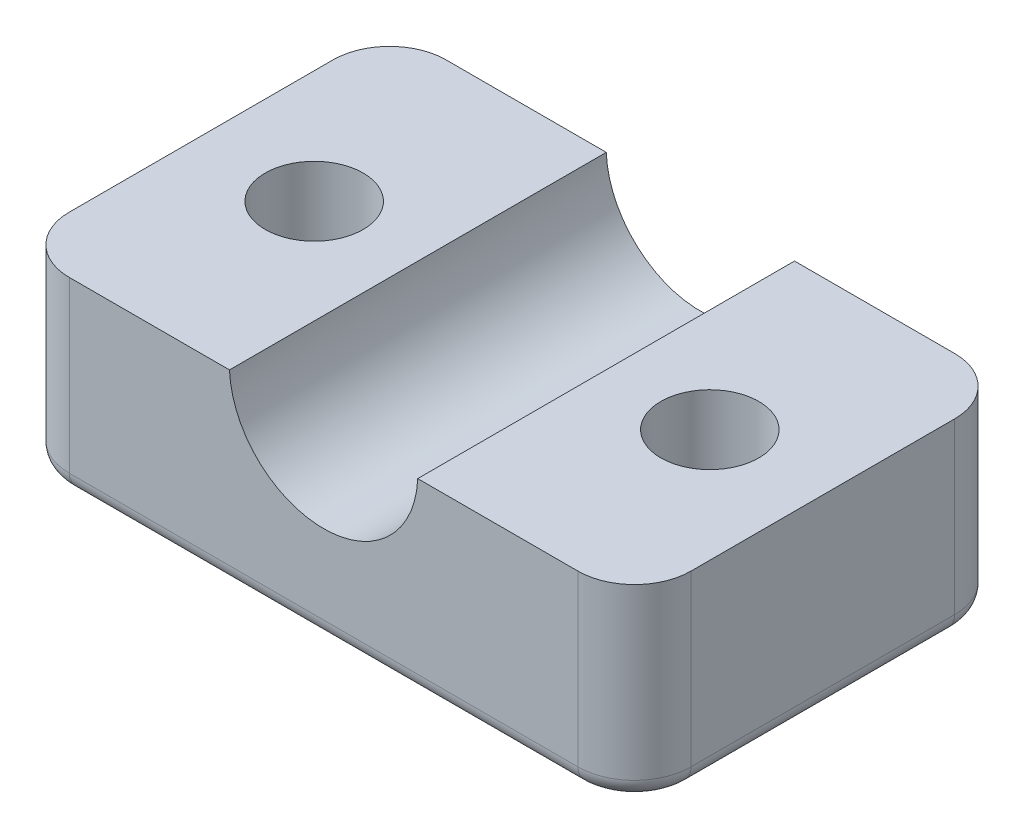
SolidWorks part; units mm, degrees
material "ABS"
ref_plane "Front Plane" through (0, 0, 0) normal (0, 0, 1) x (1, 0, 0)
ref_plane "Top Plane" through (0, 0, 0) normal (0, 1, 0) x (1, 0, 0)
ref_plane "Right Plane" through (0, 0, 0) normal (1, 0, 0) x (0, 0, -1)
sketch "Sketch1" plane through (0, 0, 0) normal (0, 1, 0) x (1, 0, 0)
  line L0 (-50.7915, 0) -> (50.7915, 0) construction
  line L1 (0, -10) -> (0, 10) construction
  line L2 (-13.5, -10) -> (13.5, -10)
  line L3 (-16.5, -7) -> (-16.5, 7)
  line L4 (-13.5, 10) -> (13.5, 10)
  line L5 (16.5, -7) -> (16.5, 7)
  line L6 (-16.5, -10) -> (16.5, 10) construction
  line L7 (-16.5, 10) -> (16.5, -10) construction
  arc A0 (-16.5, -7) -> (-13.5, -10) centre (-13.5, -7) ccw
  arc A1 (13.5, -10) -> (16.5, -7) centre (13.5, -7) ccw
  arc A2 (16.5, 7) -> (13.5, 10) centre (13.5, 7) ccw
  arc A3 (-13.5, 10) -> (-16.5, 7) centre (-13.5, 7) ccw
  circle A4 centre (10.5, 0) radius 2.6
  circle A5 centre (-10.5, 0) radius 2.6
  point P3 (0, 0)
  dimension "D3" = 3
  dimension "D4" = 5.2
  dimension "D5" = 10.5
  dimension "D1" = 33
  dimension "D2" = 20
extrude "Boss-Extrude3" add sketch "Sketch1" along normal blind 10
sketch "Sketch5" plane through (0, 0, -10) normal (0, 0, -1) x (-1, 0, 0)
  line L0 (0, 0) -> (0, 17.6887) construction
  line L1 (-13.5, 0) -> (13.5, 0) construction
  circle A0 centre (0, 10.2) radius 5
  dimension "D1" = 10.2
  dimension "D2" = 10
extrude "Cut-Extrude3" cut sketch "Sketch5" against normal up to surface (20 mm away) up to face at (0, 5, 10)
fillet "Fillet2" radius 1 8 edges at (-15.6213, 0, 9.1213) (-16.5, 0, 0) (-15.6213, 0, -9.1213) (0, 0, -10) (15.6213, 0, -9.1213) (16.5, 0, 0) (15.6213, 0, 9.1213) (0, 0, 10)
